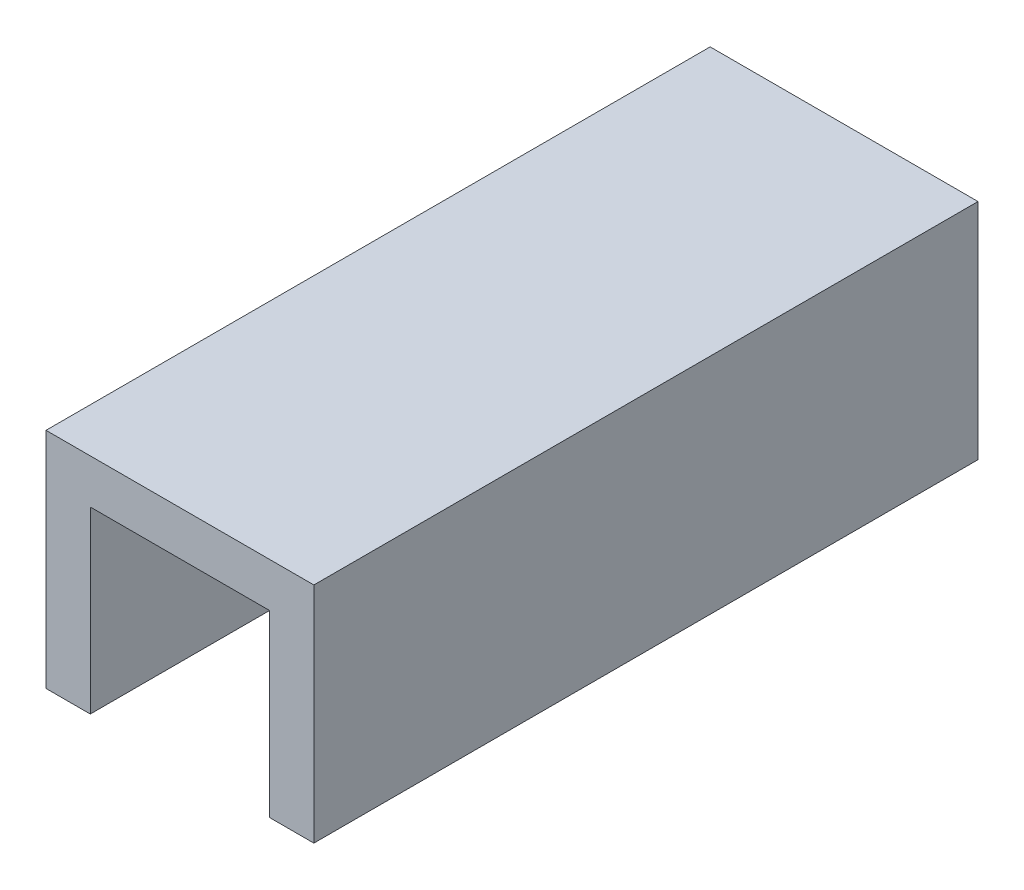
SolidWorks part; units mm, degrees
material "Roble"
ref_plane "Alzado" through (0, 0, 0) normal (0, 0, 1) x (1, 0, 0)
ref_plane "Planta" through (0, 0, 0) normal (0, 1, 0) x (1, 0, 0)
ref_plane "Vista lateral" through (0, 0, 0) normal (1, 0, 0) x (0, 0, -1)
sketch "Croquis1" plane through (0, 0, 0) normal (0, 0, 1) x (1, 0, 0)
  line L0 (-60.5, -40.5) -> (-60.5, 60.5)
  line L1 (-40.5, -40.5) -> (40.5, -40.5) construction
  line L2 (-40.5, -40.5) -> (-40.5, 40.5)
  line L3 (-40.5, 40.5) -> (40.5, 40.5)
  line L4 (40.5, -40.5) -> (40.5, 40.5)
  line L5 (-40.5, -40.5) -> (40.5, 40.5) construction
  line L6 (-40.5, 40.5) -> (40.5, -40.5) construction
  line L7 (-60.5, 60.5) -> (60.5, 60.5)
  line L8 (60.5, -40.5) -> (60.5, 60.5)
  line L9 (-60.5, -40.5) -> (-40.5, -40.5)
  line L10 (40.5, -40.5) -> (60.5, -40.5)
  point P0 (0, 0)
  point P5 (40.5, 0)
  dimension "D1" = 81
  dimension "D2" = 81
  dimension "D3" = 20
extrude "Saliente-Extruir1" add sketch "Croquis1" along normal blind 300
